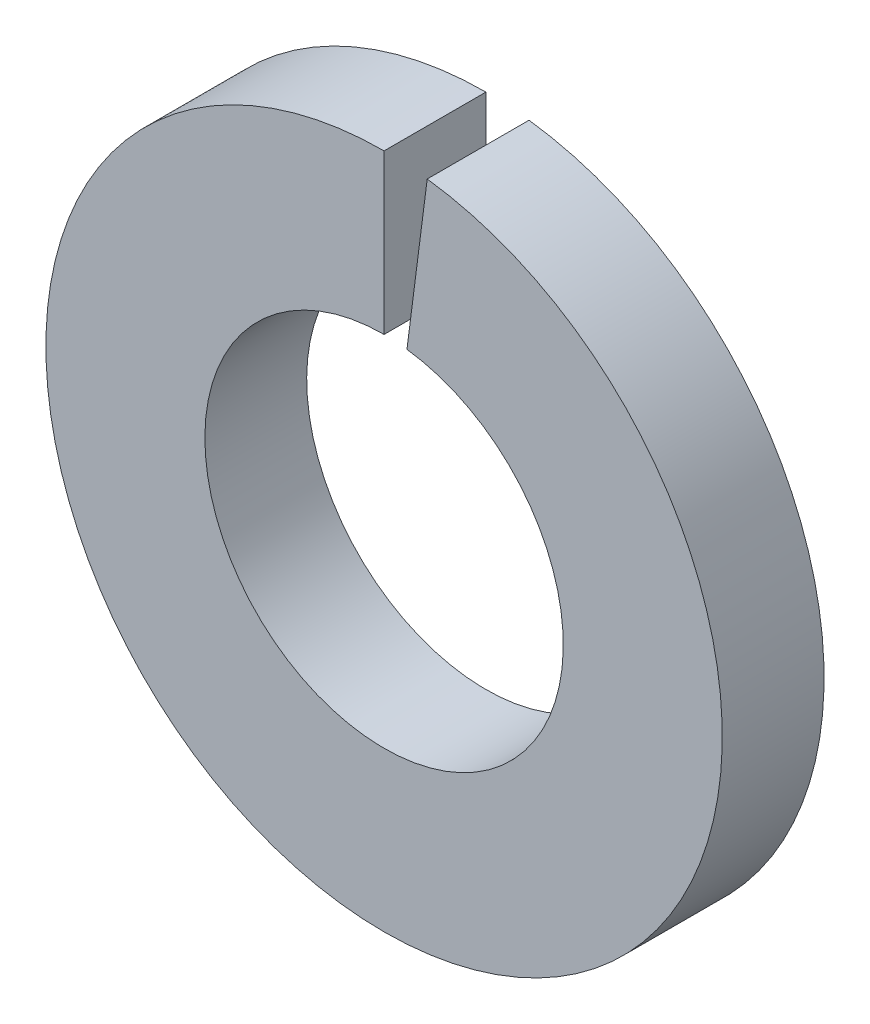
SolidWorks part; units mm, degrees
ref_plane "Front Plane" through (0, 0, 0) normal (0, 0, 1) x (1, 0, 0)
ref_plane "Top Plane" through (0, 0, 0) normal (0, 1, 0) x (1, 0, 0)
ref_plane "Right Plane" through (0, 0, 0) normal (1, 0, 0) x (0, 0, -1)
sketch "Sketch1" plane through (0, 0, 0) normal (0, 0, 1) x (1, 0, 0)
  circle A0 centre (0, 0) radius 3.2639
  circle A1 centre (0, 0) radius 6.1595
extrude "Extrude1" add sketch "Sketch1" along normal blind 1.8542
sketch "Sketch2" plane through (0, 0, 1.8542) normal (0, 0, 1) x (1, 0, 0)
  line L0 (0, 0) -> (0, 6.1595)
  line L1 (0, 0) -> (0.7859, 6.1092)
  circle A0 centre (0, 0) radius 6.1595 construction
  arc A1 (0, 6.1595) -> (0.7859, 6.1092) centre (0, 0) cw
extrude "Extrude2" cut sketch "Sketch2" against normal blind 1.8542
